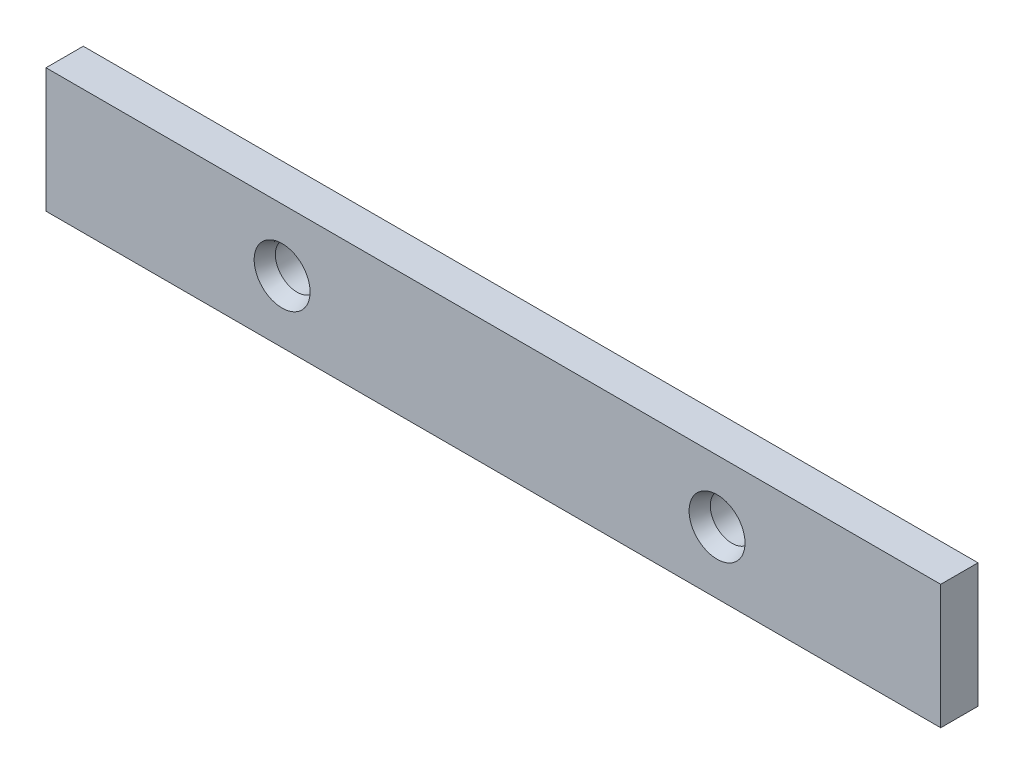
SolidWorks part; units mm, degrees
ref_plane "Front Plane" through (0, 0, 0) normal (0, 0, 1) x (1, 0, 0)
ref_plane "Top Plane" through (0, 0, 0) normal (0, 1, 0) x (1, 0, 0)
ref_plane "Right Plane" through (0, 0, 0) normal (1, 0, 0) x (0, 0, -1)
sketch "Sketch1" plane through (0, 0, 0) normal (0, 0, 1) x (1, 0, 0)
  line L1 (-72, 10) -> (72, 10)
  line L2 (-72, 10) -> (-72, -10)
  line L3 (-72, -10) -> (72, -10)
  line L4 (72, 10) -> (72, -10)
  line L5 (-72, 10) -> (72, -10) construction
  line L6 (-72, -10) -> (72, 10) construction
  point P0 (0, 0)
  dimension "D1" = 144
  dimension "D2" = 20
extrude "Boss-Extrude1" add sketch "Sketch1" along normal mid plane 6
hole_wizard "Hole1" positions "Sketch7" profile "Sketch6" legacy
sketch "Sketch7" plane through (0, 0, 3) normal (0, 0, 1) x (1, 0, 0)
  line L0 (-72, 10) -> (-72, -10) construction
  point P0 (-34, 0)
  dimension "D1" = 38
sketch "Sketch6" plane through (-34, 0, 3) normal (1, 0, 0) x (0, -1, 0)
  line L0 (0, 0) -> (0, 6)
  line L1 (0, 6) -> (3.5, 6)
  line L2 (3.5, 6) -> (3.5, 2.4142)
  line L3 (3.5, 2.4142) -> (4.5, 0)
  line L4 (4.5, 0) -> (0, 0)
  line L5 (0, -6.4453) -> (0, 115.525) construction
  line L6 (-3.5, 2.4142) -> (-4.5, 0) construction
  dimension "Diameter" = 7
  dimension "Depth" = 6
  dimension "C-Sink Angle" = 45
  dimension "C-Sink Diameter" = 9
pattern_linear "LPattern1" count 2 spacing 70 along (1, 0, 0) of "Hole1"
